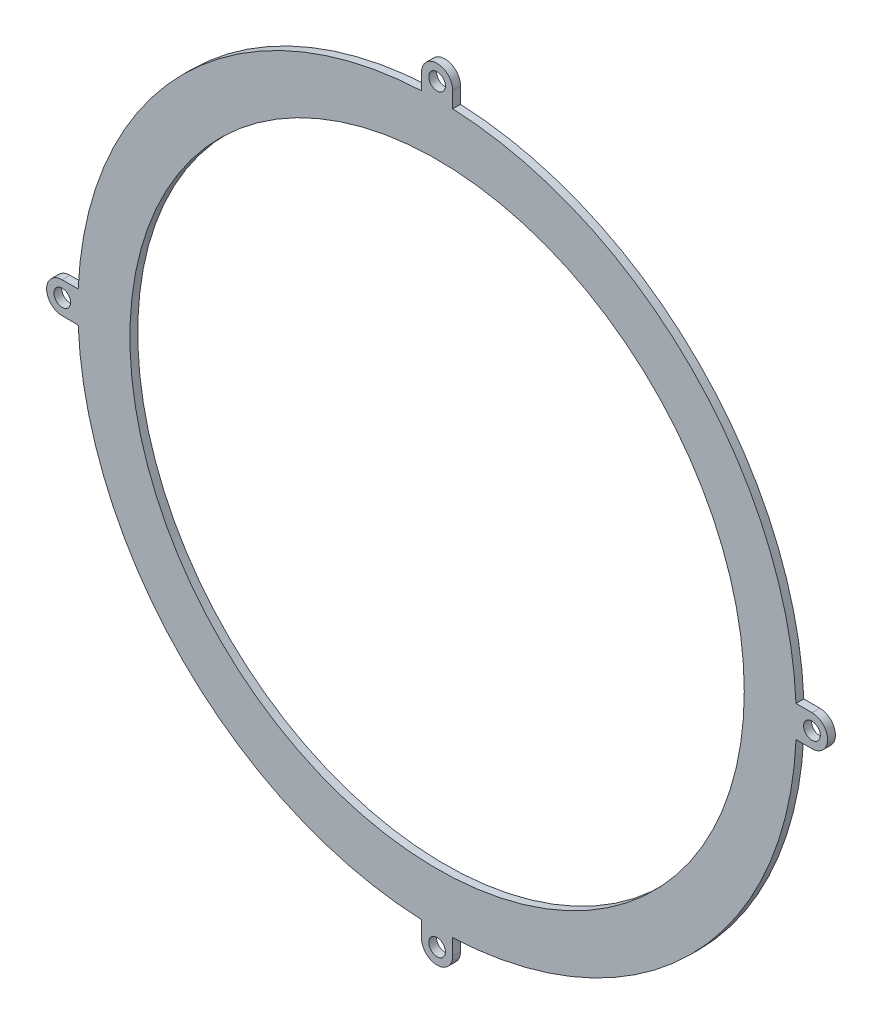
SolidWorks part; units mm, degrees
ref_plane "Front Plane" through (0, 0, 0) normal (0, 0, 1) x (1, 0, 0)
ref_plane "Top Plane" through (0, 0, 0) normal (0, 1, 0) x (1, 0, 0)
ref_plane "Right Plane" through (0, 0, 0) normal (1, 0, 0) x (0, 0, -1)
sketch "Sketch1" plane through (0, 0, 0) normal (0, 0, 1) x (1, 0, 0)
  line L0 (68.9348, -3) -> (72, -3)
  line L1 (-3, 72) -> (-3, 68.9348)
  line L2 (72, 3) -> (68.9348, 3)
  line L3 (3, 68.9348) -> (3, 72)
  line L4 (-3, -68.9348) -> (-3, -72)
  line L5 (3, -72) -> (3, -68.9348)
  line L6 (-68.9348, 3) -> (-72, 3)
  line L7 (-72, -3) -> (-68.9348, -3)
  arc A0 (-3, 68.9348) -> (-68.9348, 3) centre (0, 0) ccw
  circle A1 centre (0, 0) radius 59
  arc A2 (3, 72) -> (-3, 72) centre (0, 72) ccw
  circle A3 centre (0, 72) radius 1.6
  arc A4 (72, -3) -> (72, 3) centre (72, 0) ccw
  circle A5 centre (72, 0) radius 1.6
  arc A6 (-3, -72) -> (3, -72) centre (0, -72) ccw
  circle A7 centre (0, -72) radius 1.6
  arc A8 (-72, 3) -> (-72, -3) centre (-72, 0) ccw
  circle A9 centre (-72, 0) radius 1.6
  arc A10 (-68.9348, -3) -> (-3, -68.9348) centre (0, 0) ccw
  arc A11 (3, -68.9348) -> (68.9348, -3) centre (0, 0) ccw
  arc A12 (68.9348, 3) -> (3, 68.9348) centre (0, 0) ccw
  point P30 (0, 0)
  dimension "D1" = 4
extrude "Boss-Extrude1" add sketch "Sketch1" along normal blind 1.5
